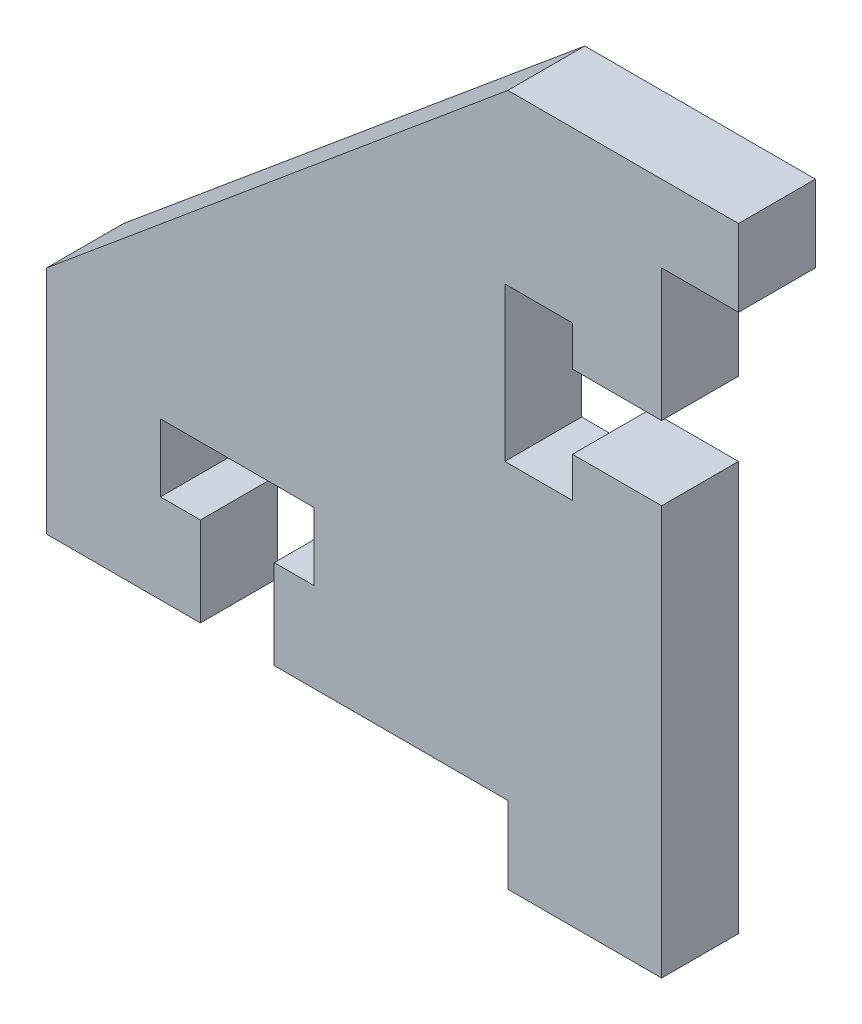
SolidWorks part; units mm, degrees
ref_plane "Front Plane" through (0, 0, 0) normal (0, 0, 1) x (1, 0, 0)
ref_plane "Top Plane" through (0, 0, 0) normal (0, 1, 0) x (1, 0, 0)
ref_plane "Right Plane" through (0, 0, 0) normal (1, 0, 0) x (0, 0, -1)
sketch "Sketch1" plane through (0, 0, 0) normal (0, 0, 1) x (1, 0, 0)
  line L0 (-6.35, 11.684) -> (3.175, 11.684)
  line L1 (3.175, 11.684) -> (3.175, 8.509)
  line L2 (3.175, 8.509) -> (0, 8.509)
  line L3 (0, 8.509) -> (0, 3.048)
  line L4 (0, 3.048) -> (-3.683, 3.048)
  line L5 (-3.683, 3.048) -> (-3.683, 4.699)
  line L6 (-3.683, 4.699) -> (-6.477, 4.699)
  line L7 (-6.477, 4.699) -> (-6.477, -1.651)
  line L8 (-6.477, -1.651) -> (-3.683, -1.651)
  line L9 (-3.683, -1.651) -> (-3.683, 0)
  line L10 (-3.683, 0) -> (0, 0)
  line L11 (0, 0) -> (0, -16.891)
  line L12 (0, -16.891) -> (-6.35, -16.891)
  line L13 (-6.35, -16.891) -> (-6.35, -13.716)
  line L14 (-6.35, -13.716) -> (-16.002, -13.716)
  line L15 (-16.002, -10.033) -> (-16.002, -13.716)
  line L16 (-16.002, -10.033) -> (-14.351, -10.033)
  line L17 (-14.351, -10.033) -> (-14.351, -7.239)
  line L18 (-14.351, -7.239) -> (-20.701, -7.239)
  line L19 (-20.701, -7.239) -> (-20.701, -10.033)
  line L20 (-20.701, -10.033) -> (-19.05, -10.033)
  line L21 (-19.05, -10.033) -> (-19.05, -13.716)
  line L22 (-19.05, -13.716) -> (-25.4, -13.716)
  line L23 (-25.4, -13.716) -> (-25.4, -4.191)
  line L24 (-25.4, -4.191) -> (-6.35, 11.684)
  dimension "D1" = 2.794
  dimension "D2" = 3.175
  dimension "D3" = 3.175
  dimension "D4" = 3.048
  dimension "D5" = 6.35
  dimension "D6" = 6.477
  dimension "D7" = 6.35
  dimension "D8" = 3.175
  dimension "D9" = 8.636
  dimension "D10" = 25.4
  dimension "D11" = 25.4
  dimension "D12" = 9.525
  dimension "D13" = 6.35
extrude "Boss-Extrude1" add sketch "Sketch1" along normal blind 3.175
